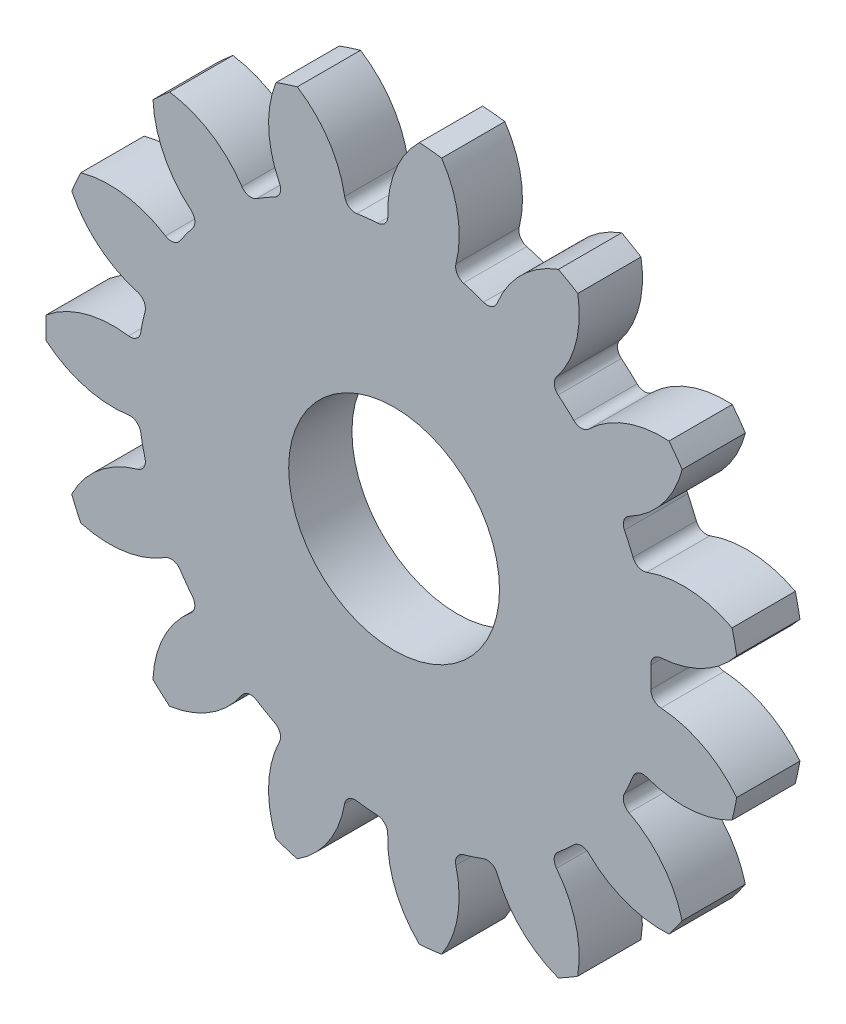
SolidWorks part; units mm, degrees
ref_plane "Alzado" through (0, 0, 0) normal (0, 0, 1) x (1, 0, 0)
ref_plane "Planta" through (0, 0, 0) normal (0, 1, 0) x (1, 0, 0)
ref_plane "Vista lateral" through (0, 0, 0) normal (1, 0, 0) x (0, 0, -1)
sketch "Croquis1" plane through (0, 0, 0) normal (0, 0, 1) x (1, 0, 0)
  circle A0 centre (0, 0) radius 16.51
  dimension "D1" = 33.02
extrude "Saliente-Extruir1" add sketch "Croquis1" along normal blind 3
sketch "Croquis2" plane through (0, 0, 3) normal (0, 0, 1) x (1, 0, 0)
  line L0 (0, 0) -> (0, 14.605) construction
  line L1 (0, 0) -> (5.9789, 16.4269) construction
  line L2 (0, 0) -> (-1.524, 14.5253) construction
  line L3 (0, 14.605) -> (4.694, 12.8965) construction
  arc A0 (1.1999, 16.4663) -> (-4.5914, 15.8587) centre (0, 0) ccw
  arc A2 (-0.2509, 12.1894) -> (-2.2845, 11.9761) centre (0, 0) ccw
  arc A3 (1.1999, 16.4663) -> (-0.2509, 12.1894) centre (4.694, 12.8965) ccw
  arc A4 (-4.5914, 15.8587) -> (-2.2845, 11.9761) centre (-7.2685, 11.6414) cw
  dimension "D2" = 24.384
  dimension "D3" = 20
  dimension "D4" = 1.524
extrude "Cortar-Extruir1" cut sketch "Croquis2" against normal through all
fillet "Redondeo1" radius 0.508 2 edges at (-0.2509, 12.1894, 1.5) (-2.2845, 11.9761, 1.5)
pattern_circular "MatrizC1" count 15 over 360 about axis through (0, 0, 0) along (0, 0, 1) of "Redondeo1", "Cortar-Extruir1"
sketch "Croquis3" plane through (0, 0, 3) normal (0, 0, 1) x (1, 0, 0)
  circle A0 centre (0, 0) radius 5
  dimension "D1" = 10
extrude "Cortar-Extruir2" cut sketch "Croquis3" against normal through all
